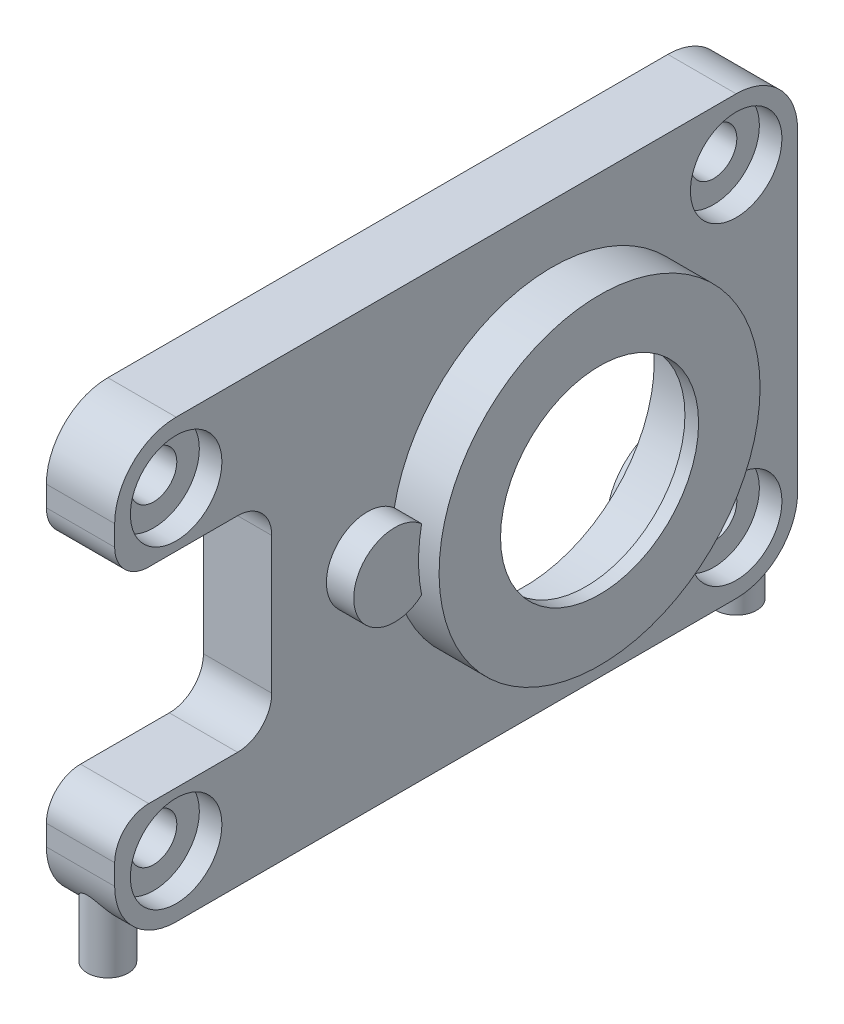
SolidWorks part; units mm, degrees
material "Delrin 2700 NC010, Low Viscosity Acetal Copolymer (SS)"
ref_plane "Front Plane" through (0, 0, 0) normal (0, 0, 1) x (1, 0, 0)
ref_plane "Top Plane" through (0, 0, 0) normal (0, 1, 0) x (1, 0, 0)
ref_plane "Right Plane" through (0, 0, 0) normal (1, 0, 0) x (0, 0, -1)
sketch "Sketch1" plane through (0, 0, 0) normal (1, 0, 0) x (0, 0, -1)
  line L0 (-25, 7.5) -> (-13.5, 7.5)
  line L1 (-25, -16) -> (25, -16)
  line L2 (-25, -16) -> (-25, 16)
  line L3 (-25, 16) -> (25, 16)
  line L4 (25, -16) -> (25, 16)
  line L5 (-25, -16) -> (25, 16) construction
  line L6 (-25, 16) -> (25, -16) construction
  line L7 (-13.5, 7.5) -> (-13.5, -7.5)
  line L8 (-13.5, -7.5) -> (-25, -7.5)
  line L9 (-13.5, 0) -> (0, 0) construction
  line L10 (0, 0) -> (25, 0) construction
  circle A0 centre (7, 0) radius 7.25
  point P0 (0, 0)
  dimension "D5" = 14.5
  dimension "D6" = 18
  dimension "D1" = 32
  dimension "D2" = 50
  dimension "D3" = 8.5
  dimension "D4" = 38.5
extrude "Boss-Extrude1" add sketch "Sketch1" along normal blind 5 contours L7 L8 L2 L1 L4 L3 L0
sketch "Sketch2" plane through (5, 0, 0) normal (1, 0, 0) x (0, 0, -1)
  line L0 (-13.5, 0) -> (25, 0) construction
  line L1 (-13.5, 7.5) -> (-13.5, -7.5) construction
  line L2 (25, -16) -> (25, 16) construction
  circle A0 centre (7, 0) radius 11.75
  circle A1 centre (7, 0) radius 7.25 construction
  circle A2 centre (7, 0) radius 7.25
  dimension "D1" = 23.5
extrude "Boss-Extrude2" add sketch "Sketch2" along normal blind 3.5
fillet "Fillet1" radius 4.5 4 edges at (2.5, 16, -25) (2.5, -16, -25) (2.5, -16, 25) (2.5, 16, 25)
fillet "Fillet2" radius 2.5 4 edges at (2.5, -7.5, 25) (2.5, -7.5, 13.5) (2.5, 7.5, 25) (2.5, 7.5, 13.5)
sketch "Sketch3" plane through (0, -16, 0) normal (0, -1, 0) x (-1, 0, 0)
  line L0 (-2.5, -25) -> (-2.5, 25) construction
  line L1 (0, -25) -> (-5, -25) construction
  line L2 (-5, 25) -> (0, 25) construction
  line L3 (0, 0) -> (-5, 0) construction
  line L4 (-5, -20.5) -> (-5, 20.5) construction
  circle A0 centre (-2.5, -23) radius 1.5
  circle A1 centre (-2.5, 23) radius 1.5
  dimension "D1" = 46
  dimension "D2" = 3
  dimension "D3" = 23
extrude "Boss-Extrude3" add sketch "Sketch3" along normal blind 2.5 and the other way up to next
hole_wizard "CBORE for M3 SBHCS1" positions "Sketch5" profile "Sketch4" counterbore size "M3" standard "ANSI Metric" end condition through all
sketch "Sketch5" plane through (5, 0, 0) normal (1, 0, 0) x (0, 0, -1)
  line L1 (-20.5, 11.5) -> (20.5, 11.5)
  line L2 (-20.5, 11.5) -> (-20.5, -11.5)
  line L3 (-20.5, -11.5) -> (20.5, -11.5)
  line L4 (20.5, 11.5) -> (20.5, -11.5)
  line L5 (-13.5, 0) -> (25, 0) construction
  line L6 (-13.5, 5) -> (-13.5, -5) construction
  line L7 (25, -11.5) -> (25, 11.5) construction
  line L10 (-20.5, 16) -> (20.5, 16) construction
  line L11 (-20.5, -16) -> (20.5, -16) construction
  point P0 (-20.5, 11.5)
  point P2 (-20.5, -11.5)
  point P4 (20.5, 11.5)
  point P6 (20.5, -11.5)
  dimension "D1" = 4.5
  dimension "D2" = 4.5
  dimension "D3" = 4.5
  dimension "D4" = 41
sketch "Sketch4" plane through (5, 11.5, 20.5) normal (0, 1, 0) x (0, 0, -1)
  line L0 (0, 0) -> (0, 5)
  line L1 (0, 5) -> (1.7, 5)
  line L3 (1.7, 5) -> (1.7, 1.65)
  line L4 (1.7, 1.65) -> (3.35, 1.65)
  line L5 (3.35, 1.65) -> (3.35, 0)
  line L7 (3.35, 0) -> (0, 0)
  line L11 (0, -6.35) -> (0, 107.95) construction
  dimension "Thru Hole Dia." = 3.4
  dimension "Thru Hole Depth" = 5
  dimension "C'Bore Dia." = 6.7
  dimension "C'Bore Depth" = 1.65
sketch "Sketch6" plane through (0, 0, 0) normal (-1, 0, 0) x (0, 0, 1)
  line L16 (11.5, 14) -> (11.5, -14)
  line L24 (16, 9.5) -> (22.5, 9.5)
  line L25 (23, 10) -> (23, 11.5)
  line L26 (20.5, 14) -> (-20.5, 14)
  line L27 (-23, 11.5) -> (-23, -11.5)
  line L28 (-20.5, -14) -> (20.5, -14)
  line L29 (23, 10) -> (23, 11.5)
  line L30 (22.5, -9.5) -> (16, -9.5)
  line L31 (11.5, -5) -> (11.5, 5)
  line L32 (16, 9.5) -> (22.5, 9.5)
  line L33 (23, -11.5) -> (23, -10)
  line L34 (20.5, 14) -> (-20.5, 14)
  line L35 (-23, 11.5) -> (-23, -11.5)
  line L36 (-20.5, -14) -> (20.5, -14)
  line L37 (23, -11.5) -> (23, -10)
  line L38 (22.5, -9.5) -> (16, -9.5)
  line L39 (11.5, -5) -> (11.5, 5)
  circle A16 centre (-20.5, -11.5) radius 4.5
  circle A17 centre (-20.5, 11.5) radius 4.5
  arc A18 (-20.5, 16) -> (-25, 11.5) centre (-20.5, 11.5) ccw construction
  arc A19 (-24.5, -13.5616) -> (-21.5, -15.8875) centre (-20.5, -11.5) ccw construction
  arc A24 (23, -10) -> (22.5, -9.5) centre (22.5, -10) ccw
  arc A25 (23, 11.5) -> (20.5, 14) centre (20.5, 11.5) ccw
  arc A26 (-20.5, 14) -> (-23, 11.5) centre (-20.5, 11.5) ccw
  arc A27 (-23, -11.5) -> (-20.5, -14) centre (-20.5, -11.5) ccw
  arc A28 (20.5, -14) -> (23, -11.5) centre (20.5, -11.5) ccw
  arc A29 (23, -10) -> (22.5, -9.5) centre (22.5, -10) ccw
  arc A30 (11.5, -5) -> (16, -9.5) centre (16, -5) ccw
  arc A31 (11.5, -5) -> (16, -9.5) centre (16, -5) ccw
  arc A32 (16, 9.5) -> (11.5, 5) centre (16, 5) ccw
  arc A33 (23, 11.5) -> (20.5, 14) centre (20.5, 11.5) ccw
  arc A34 (-20.5, 14) -> (-23, 11.5) centre (-20.5, 11.5) ccw
  arc A35 (-23, -11.5) -> (-20.5, -14) centre (-20.5, -11.5) ccw
  arc A36 (20.5, -14) -> (23, -11.5) centre (20.5, -11.5) ccw
  arc A37 (16, 9.5) -> (11.5, 5) centre (16, 5) ccw
  arc A38 (22.5, 9.5) -> (23, 10) centre (22.5, 10) ccw
  arc A39 (22.5, 9.5) -> (23, 10) centre (22.5, 10) ccw
  circle M21 centre (-7, 0) radius 7.25
  dimension "D1" = 2
extrude "Cut-Extrude1" cut sketch "Sketch6" against normal blind 3 contours A17 L35 A16 L36 L16 L34 M21
sketch "Sketch7" plane through (3, 0, 0) normal (-1, 0, 0) x (0, 0, 1)
  circle A0 centre (-7, 0) radius 9.5
  dimension "D1" = 19
extrude "Cut-Extrude2" cut sketch "Sketch7" against normal blind 4.5
sketch "Sketch10" plane through (5, 0, 0) normal (1, 0, 0) x (0, 0, -1)
  line L0 (-13.5, 0) -> (7, 0) construction
  line L1 (-13.5, 5) -> (-13.5, -5) construction
  circle A0 centre (-6.5, 0) radius 3
  dimension "D1" = 6
  dimension "D2" = 13.5
extrude "Boss-Extrude5" add sketch "Sketch10" along normal blind 2
sketch "Sketch11" plane through (3, 0, 0) normal (-1, 0, 0) x (0, 0, 1)
  arc A0 (4.5301, -2.2626) -> (4.5301, 2.2626) centre (6.5, 0) ccw construction
  arc A1 (4.5301, -2.2626) -> (4.5301, 2.2626) centre (6.5, 0) ccw construction
  circle A2 centre (6.5, 0) radius 3
extrude "Boss-Extrude6" add sketch "Sketch11" along normal blind 0.5
sketch "Sketch12" plane through (2.5, 0, 0) normal (-1, 0, 0) x (0, 0, 1)
  circle A0 centre (6.5, 0) radius 1.5
  dimension "D1" = 3
extrude "Cut-Extrude4" cut sketch "Sketch12" against normal blind 4
move or copy body "Body-Move/Copy1" [suppressed] bodies to move or copy 121
